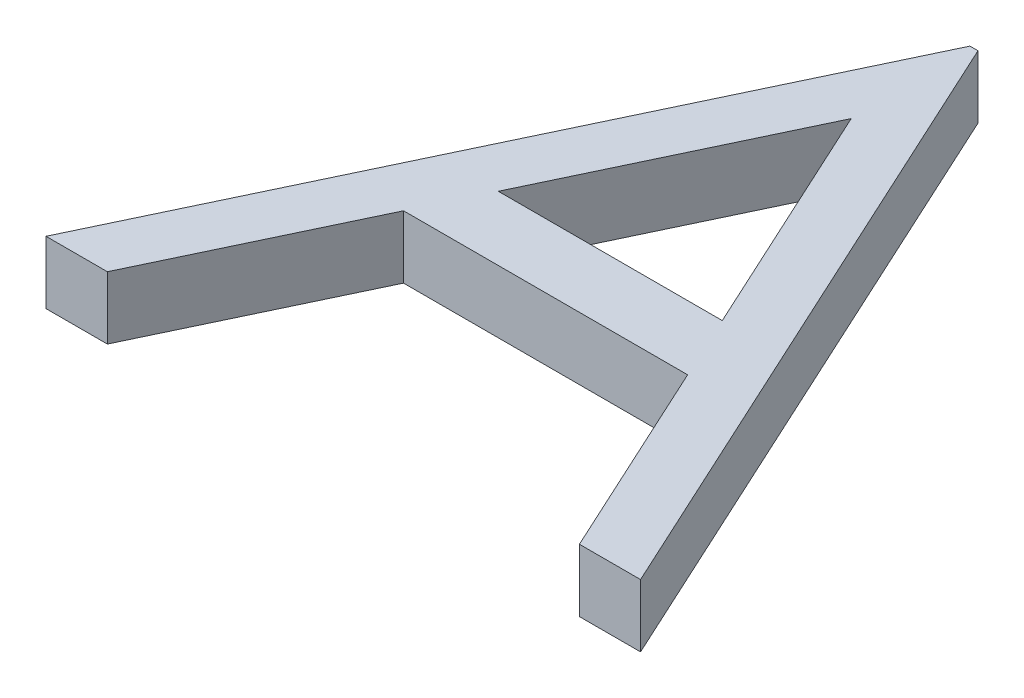
SolidWorks part; units mm, degrees
ref_plane "Front Plane" through (0, 0, 0) normal (0, 0, 1) x (1, 0, 0)
ref_plane "Top Plane" through (0, 0, 0) normal (0, 1, 0) x (1, 0, 0)
ref_plane "Right Plane" through (0, 0, 0) normal (1, 0, 0) x (0, 0, -1)
sketch "Sketch3" plane through (0, 0, 0) normal (0, 1, 0) x (1, 0, 0)
  text T0 "A" font "Century Gothic" height 25.4
extrude "Boss-Extrude2" add sketch "Sketch3" along normal blind 2.54
